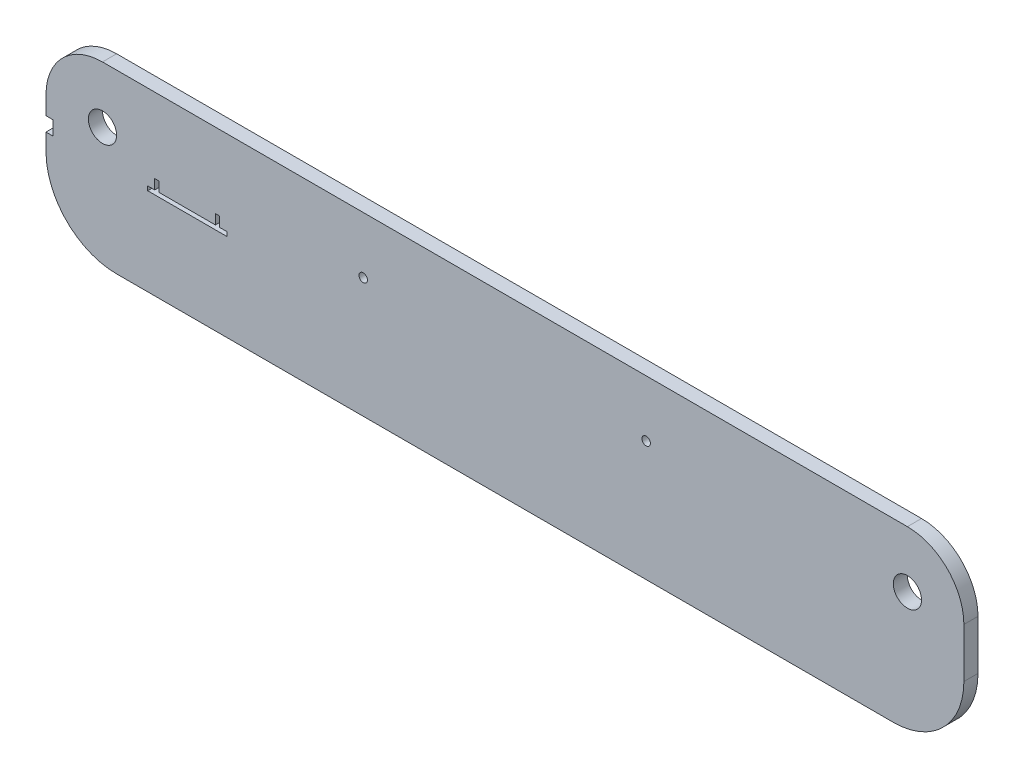
SolidWorks part; units mm, degrees
ref_plane "Front Plane" through (0, 0, 0) normal (0, 0, 1) x (1, 0, 0)
ref_plane "Top Plane" through (0, 0, 0) normal (0, 1, 0) x (1, 0, 0)
ref_plane "Right Plane" through (0, 0, 0) normal (1, 0, 0) x (0, 0, -1)
sketch "Sketch1" plane through (0, 0, 0) normal (0, 0, 1) x (1, 0, 0)
  line L1 (-47.1041, 88.3097) -> (602.8959, 88.3097)
  line L2 (-47.1041, 88.3097) -> (-47.1041, -36.6903)
  line L3 (-47.1041, -36.6903) -> (602.8959, -36.6903)
  line L4 (602.8959, 88.3097) -> (602.8959, -36.6903)
extrude "Boss-Extrude1" add sketch "Sketch1" along normal blind 10
sketch "Sketch2" plane through (0, 0, 10) normal (0, 0, 1) x (1, 0, 0)
  circle A0 centre (-7.1041, 48.3097) radius 10
extrude "Cut-Extrude2" cut sketch "Sketch2" against normal blind 10 contours A0
sketch "Sketch3" plane through (0, 0, 10) normal (0, 0, 1) x (1, 0, 0)
  circle A1 centre (562.8959, 48.3097) radius 10
extrude "Cut-Extrude3" cut sketch "Sketch3" against normal blind 10
sketch "Sketch4" plane through (0, 0, 10) normal (0, 0, 1) x (1, 0, 0)
  line L5 (32.8959, 68.3097) -> (72.8959, 68.3097)
  line L6 (72.8959, 68.3097) -> (72.8959, 28.3097)
  line L7 (72.8959, 28.3097) -> (32.8959, 28.3097)
  line L11 (29.8959, 71.3097) -> (75.8959, 71.3097)
  line L12 (75.8959, 71.3097) -> (75.8959, 25.3097)
  line L13 (75.8959, 25.3097) -> (29.8959, 25.3097)
  line L16 (32.8959, 28.3097) -> (32.8959, 35.3097)
  line L17 (29.8959, 48.3097) -> (29.8959, 71.3097) construction
  line L18 (29.8959, 25.3097) -> (29.8959, 48.3097) construction
  line L19 (32.8959, 28.3097) -> (32.8959, 48.3097) construction
  line L20 (32.8959, 48.3097) -> (32.8959, 68.3097) construction
  line L21 (32.8959, 35.3097) -> (29.8959, 35.3097)
  line L22 (29.8959, 35.3097) -> (29.8959, 25.3097)
  line L23 (29.8959, 71.3097) -> (29.8959, 61.3097)
  line L24 (29.8959, 61.3097) -> (32.8959, 61.3097)
  line L25 (32.8959, 61.3097) -> (32.8959, 68.3097)
  dimension "D1" = 3
extrude "Boss-Extrude3" add sketch "Sketch4" along normal blind 20
sketch "Sketch5" plane through (0, 0, 30) normal (0, 0, 1) x (1, 0, 0)
  line L1 (75.8959, 71.3097) -> (29.8959, 71.3097) construction
  line L2 (39.8959, 71.3097) -> (39.8959, 68.3097)
  line L3 (32.8959, 68.3097) -> (72.8959, 68.3097) construction
  line L4 (39.8959, 68.3097) -> (65.8959, 68.3097)
  line L5 (32.8959, 68.3097) -> (72.8959, 68.3097) construction
  line L6 (65.8959, 68.3097) -> (65.8959, 71.3097)
  line L7 (65.8959, 71.3097) -> (39.8959, 71.3097)
extrude "Cut-Extrude4" cut sketch "Sketch5" against normal blind 20
sketch "Sketch7" plane through (0, 0, 10) normal (0, 0, 1) x (1, 0, 0)
  line L0 (527.8959, -36.6903) -> (463.8959, -36.6903)
  line L5 (-47.1041, -36.6903) -> (602.8959, -36.6903) construction
  line L6 (463.8959, -36.6903) -> (463.8959, 25.3097)
  line L7 (527.8959, -36.6903) -> (527.8959, 25.3097)
  line L8 (458.8959, 25.3097) -> (458.8959, -36.6903)
  line L9 (458.8959, -36.6903) -> (394.8959, -36.6903)
  line L10 (394.8959, -36.6903) -> (394.8959, 25.3097)
  line L11 (602.8959, -36.6903) -> (602.8959, 88.3097) construction
  line L12 (525.8959, -34.6903) -> (525.8959, 25.3097)
  line L13 (525.8959, -34.6903) -> (465.8959, -34.6903)
  line L14 (465.8959, -34.6903) -> (465.8959, 25.3097)
  line L15 (456.8959, 25.3097) -> (456.8959, -34.6903)
  line L16 (456.8959, -34.6903) -> (396.8959, -34.6903)
  line L17 (396.8959, -34.6903) -> (396.8959, 25.3097)
  line L18 (525.8959, 25.3097) -> (527.8959, 25.3097)
  line L19 (465.8959, 25.3097) -> (463.8959, 25.3097)
  line L20 (456.8959, 25.3097) -> (458.8959, 25.3097)
  line L21 (394.8959, 25.3097) -> (396.8959, 25.3097)
  dimension "D1" = 75
  dimension "D2" = 5
  dimension "D3" = 64
  dimension "D4" = 64
  dimension "D5" = 2
extrude "Boss-Extrude4" add sketch "Sketch7" along normal blind 20
sketch "Sketch8" plane through (0, 0, 10) normal (0, 0, 1) x (1, 0, 0)
  circle A0 centre (177.5091, 48.3097) radius 3
  circle A1 centre (377.8959, 48.3097) radius 3
extrude "Cut-Extrude5" cut sketch "Sketch8" against normal blind 20
fillet "Fillet1" radius 50 1 edges at (602.8959, -36.6903, 5)
fillet "Fillet2" radius 40 1 edges at (602.8959, 88.3097, 5)
fillet "Fillet3" radius 50 1 edges at (-47.1041, -36.6903, 5)
fillet "Fillet4" radius 40 1 edges at (-47.1041, 88.3097, 5)
sketch "Sketch9" plane through (-47.1041, 0, 0) normal (-1, 0, 0) x (0, 0, 1)
  circle A0 centre (5, 30.3097) radius 3
extrude "Cut-Extrude6" cut sketch "Sketch9" against normal blind 10
sketch "Sketch10" plane through (-47.1041, 0, 0) normal (-1, 0, 0) x (0, 0, 1)
  line L0 (0, 48.3097) -> (0, 13.3097) construction
  line L1 (10, 25.3097) -> (0, 25.3097)
  line L2 (10, 25.3097) -> (10, 35.3097)
  line L3 (10, 35.3097) -> (0, 35.3097)
  line L4 (0, 25.3097) -> (0, 35.3097)
extrude "Cut-Extrude7" cut sketch "Sketch10" against normal blind 5
sketch "Sketch11" plane through (0, 0, 30) normal (0, 0, 1) x (1, 0, 0)
  line L0 (29.8959, 35.3097) -> (32.8959, 35.3097)
  line L1 (32.8959, 35.3097) -> (32.8959, 28.3097)
  line L2 (32.8959, 28.3097) -> (72.8959, 28.3097)
  line L3 (72.8959, 28.3097) -> (72.8959, 35.3097)
  line L4 (72.8959, 68.3097) -> (72.8959, 28.3097) construction
  line L5 (72.8959, 35.3097) -> (75.8959, 35.3097)
  line L6 (75.8959, 25.3097) -> (75.8959, 71.3097) construction
  line L8 (75.8959, 25.3097) -> (29.8959, 25.3097)
  line L9 (29.8959, 25.3097) -> (24.8959, 25.3097)
  line L10 (24.8959, 25.3097) -> (24.8959, 28.3097)
  line L11 (24.8959, 28.3097) -> (29.8959, 28.3097)
  line L12 (29.8959, 35.3097) -> (29.8959, 25.3097) construction
  line L13 (29.8959, 28.3097) -> (29.8959, 35.3097)
  line L14 (75.8959, 25.3097) -> (80.8959, 25.3097)
  line L15 (80.8959, 25.3097) -> (80.8959, 28.3097)
  line L16 (80.8959, 28.3097) -> (75.8959, 28.3097)
  line L17 (75.8959, 28.3097) -> (75.8959, 35.3097)
extrude "Cut-Extrude8" cut sketch "Sketch11" against normal blind 30 contours L5 L17 L16 L15 L14 L8 L9 L10 L11 L13 L0 L1 L2 L3
sketch "Sketch12" plane through (0, -36.6903, 0) normal (0, -1, 0) x (1, 0, 0)
  line L1 (394.8959, 30) -> (527.8959, 30)
  line L2 (394.8959, 30) -> (394.8959, 10)
  line L3 (394.8959, 10) -> (527.8959, 10)
  line L4 (527.8959, 30) -> (527.8959, 10)
extrude "Cut-Extrude9" cut sketch "Sketch12" against normal blind 100
sketch "Sketch13" plane through (75.8959, 0, 0) normal (1, 0, 0) x (0, 0, -1)
  line L1 (-30, 71.3097) -> (-10, 71.3097)
  line L2 (-30, 71.3097) -> (-30, 35.3097)
  line L3 (-30, 35.3097) -> (-10, 35.3097)
  line L4 (-10, 71.3097) -> (-10, 35.3097)
extrude "Cut-Extrude10" cut sketch "Sketch13" against normal blind 100
